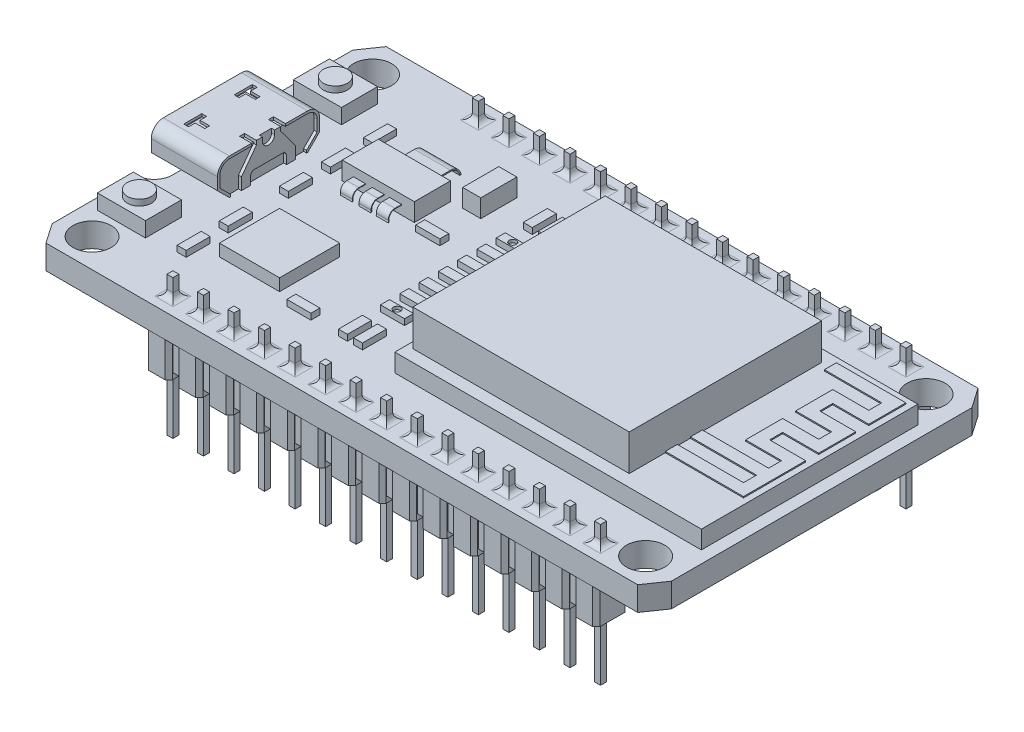
SolidWorks part; units mm, degrees
ref_plane "Alzado" through (0, 0, 0) normal (0, 0, 1) x (1, 0, 0)
ref_plane "Planta" through (0, 0, 0) normal (0, 1, 0) x (1, 0, 0)
ref_plane "Vista lateral" through (0, 0, 0) normal (1, 0, 0) x (0, 0, -1)
sketch "Croquis1" plane through (0, 0, 0) normal (0, 1, 0) x (1, 0, 0)
  line L1 (25.75, 14.15) -> (-25.75, 14.15)
  line L2 (25.75, 14.15) -> (25.75, -14.15)
  line L3 (25.75, -14.15) -> (-25.75, -14.15)
  line L4 (-25.75, 14.15) -> (-25.75, -14.15)
  line L5 (25.75, 14.15) -> (-25.75, -14.15) construction
  line L6 (25.75, -14.15) -> (-25.75, 14.15) construction
  point P0 (0, 0)
  dimension "D1" = 28.3
  dimension "D2" = 51.5
extrude "Saliente-Extruir1" add sketch "Croquis1" along normal blind 2
sketch "Croquis2" plane through (0, 2, 0) normal (0, 1, 0) x (1, 0, 0)
  line L0 (-23.1625, 11.5625) -> (22.875, 11.5625) construction
  line L1 (-23.1625, 11.5625) -> (-25.75, 11.5625) construction
  line L2 (-25.75, 14.15) -> (-25.75, -14.15) construction
  line L3 (-25.75, 11.5625) -> (-24.75, 11.5625) construction
  line L4 (24.4625, 11.5625) -> (25.75, 11.5625) construction
  line L5 (25.75, -14.15) -> (25.75, 14.15) construction
  line L6 (-23.1625, 13.15) -> (-23.1625, 14.15) construction
  line L8 (-23.1625, 11.5625) -> (-23.1625, -11.7625) construction
  line L9 (-23.1625, -11.7625) -> (22.875, -11.7625) construction
  line L10 (25.75, 14.15) -> (-25.75, 14.15) construction
  circle A0 centre (-23.1625, 11.5625) radius 1.5875
  circle A1 centre (22.875, 11.5625) radius 1.5875
  circle A2 centre (-23.1625, -11.7625) radius 1.5875
  circle A3 centre (22.875, -11.7625) radius 1.5875
  point P6 (-0.1437, 11.5625)
  dimension "D1" = 3.175
  dimension "D3" = 1
  dimension "D2" = 46.0375
  dimension "D4" = 1.2875
  dimension "D5" = 23.325
  dimension "D6" = 1
extrude "Cortar-Extruir1" cut sketch "Croquis2" against normal blind 2
sketch "Croquis13" plane through (0, 2, 0) normal (0, 1, 0) x (1, 0, 0)
  line L0 (25.75, 12.5) -> (25.75, -12.5)
  line L1 (25.75, -14.15) -> (25.75, 14.15) construction
  line L2 (-24.6062, -14.15) -> (24.6062, -14.15)
  line L3 (-25.75, -14.15) -> (25.75, -14.15) construction
  line L4 (-24.6062, 14.15) -> (24.6062, 14.15)
  line L5 (25.75, 14.15) -> (-25.75, 14.15) construction
  line L6 (24.6062, 14.15) -> (25.75, 12.5)
  line L7 (25.75, -12.5) -> (24.6062, -14.15)
  line L8 (-25.75, 12.5) -> (-25.75, 5.5)
  line L10 (-25.75, 14.15) -> (-25.75, -14.15) construction
  line L11 (-24.6062, 14.15) -> (-25.75, 12.5)
  line L12 (-25.75, -12.5) -> (-24.6062, -14.15)
  line L13 (-24.25, 4) -> (-24.25, -4)
  line L14 (-25.75, -5.5) -> (-25.75, -12.5)
  arc A0 (-24.25, 4) -> (-25.75, 5.5) centre (-25.75, 4) ccw
  arc A1 (-25.75, -5.5) -> (-24.25, -4) centre (-25.75, -4) ccw
  point P5 (25.75, 0)
  point P11 (0, -14.15)
  point P16 (0, 14.15)
  point P19 (-25.75, 0)
  point P24 (-24.25, 0)
  dimension "D1" = 25
  dimension "D2" = 49.2125
  dimension "D3" = 25
  dimension "D4" = 8
  dimension "D5" = 1.5
extrude "Cortar-Extruir2" cut sketch "Croquis13" against normal blind 3 flip side to cut
sketch "Croquis3" plane through (0, 2, 0) normal (0, 1, 0) x (1, 0, 0)
  line L0 (25.75, -12.5) -> (25.75, 12.5) construction
  line L1 (-0.75, -9) -> (24.75, -9)
  line L2 (-0.75, -9) -> (-0.75, 9)
  line L3 (-0.75, 9) -> (24.75, 9)
  line L4 (24.75, -9) -> (24.75, 9)
  line L5 (-0.75, -9) -> (24.75, 9) construction
  line L6 (-0.75, 9) -> (24.75, -9) construction
  point P0 (12, 0)
  dimension "D1" = 18
  dimension "D2" = 25.5
  dimension "D3" = 1
extrude "Saliente-Extruir2" add sketch "Croquis3" along normal blind 1.5
sketch "Croquis4" plane through (0, 3.5, 0) normal (0, 1, 0) x (1, 0, 0)
  line L0 (17.75, 0) -> (24.75, 0) construction
  line L1 (17.75, 8) -> (-0.25, 8)
  line L2 (17.75, 8) -> (17.75, -8)
  line L3 (17.75, -8) -> (-0.25, -8)
  line L4 (-0.25, 8) -> (-0.25, -8)
  line L5 (17.75, 8) -> (-0.25, -8) construction
  line L6 (17.75, -8) -> (-0.25, 8) construction
  line L7 (24.75, -9) -> (24.75, 9) construction
  point P0 (8.75, 0)
  dimension "D1" = 16
  dimension "D2" = 18
  dimension "D3" = 7
extrude "Saliente-Extruir3" add sketch "Croquis4" along normal blind 3
sketch "Croquis5" plane through (0, 2, 0) normal (0, 1, 0) x (1, 0, 0)
  line L0 (-15.75, 12.7) -> (-15.25, 12.7) construction
  line L2 (-15.25, 12.95) -> (-15.75, 12.95)
  line L3 (-15.25, 12.95) -> (-15.25, 12.45)
  line L4 (-15.25, 12.45) -> (-15.75, 12.45)
  line L5 (-15.75, 12.95) -> (-15.75, 12.45)
  line L6 (-15.25, 12.95) -> (-15.75, 12.45) construction
  line L7 (-15.25, 12.45) -> (-15.75, 12.95) construction
  line L63 (-15.75, 12.7) -> (-25.75, 12.7) construction
  line L64 (-15.5, -12.7) -> (-15.5, 12.7) construction
  line L65 (-25.75, 12.5) -> (-25.75, 5.5) construction
  line L70 (-15.25, -12.45) -> (-15.75, -12.45)
  line L71 (-15.25, -12.45) -> (-15.25, -12.95)
  line L132 (-15.25, -12.95) -> (-15.75, -12.95)
  line L133 (-15.75, -12.45) -> (-15.75, -12.95)
  line L134 (-15.25, -12.45) -> (-15.75, -12.95) construction
  line L135 (-15.25, -12.95) -> (-15.75, -12.45) construction
  point P2 (-15.5, 12.7)
  point P13 (-15.5, 0)
  dimension "D1" = 25.4
  dimension "D2" = 0.5
  dimension "D3" = 0.5
  dimension "D5" = 10
extrude "Saliente-Extruir4" add sketch "Croquis5" against normal blind 10 and the other way blind 1.5875
sketch "Croquis6" plane through (0, 0, 0) normal (0, -1, 0) x (1, 0, 0)
  line L0 (-15.25, -12.95) -> (-15.75, -12.45) construction
  line L1 (-15.25, 12.45) -> (-15.75, 12.95) construction
  line L2 (-15.75, -12.45) -> (-15.25, -12.45) construction
  line L3 (-15.75, 12.95) -> (-15.25, 12.95) construction
  line L4 (-15.75, 12.95) -> (-15.25, 12.95) construction
  line L5 (-16.5, -11.35) -> (-14.5, -11.35)
  line L6 (-16.5, -11.35) -> (-16.5, -14.05)
  line L7 (-16.5, -14.05) -> (-14.5, -14.05)
  line L8 (-14.5, -11.35) -> (-14.5, -14.05)
  line L9 (-16.5, -11.35) -> (-14.5, -14.05) construction
  line L10 (-16.5, -14.05) -> (-14.5, -11.35) construction
  line L12 (-14.5, 14.05) -> (-16.5, 14.05)
  line L13 (-14.5, 14.05) -> (-14.5, 11.35)
  line L14 (-14.5, 11.35) -> (-16.5, 11.35)
  line L15 (-16.5, 14.05) -> (-16.5, 11.35)
  line L16 (-14.5, 14.05) -> (-16.5, 11.35) construction
  line L17 (-14.5, 11.35) -> (-16.5, 14.05) construction
  point P4 (-15.5, -12.7)
  point P5 (-15.5, -12.7)
  point P8 (-15.5, -12.7)
  point P19 (-15.5, 12.7)
  point P20 (-15.5, 12.7)
  dimension "D1" = 2.7
  dimension "D2" = 2
extrude "Saliente-Extruir5" add sketch "Croquis6" along normal blind 3
chamfer "Chaflán1" distance 0.3 angle 45 8 edges at (-16.5, -1.5, -14.05) (-16.5, -1.5, -11.35) (-14.5, -1.5, -11.35) (-14.5, -1.5, -14.05) (-16.5, -1.5, 11.35) (-14.5, -1.5, 11.35) (-14.5, -1.5, 14.05) (-16.5, -1.5, 14.05)
sketch "Croquis7" plane through (0, 0, 0) normal (0, -1, 0) x (1, 0, 0)
  line L0 (-14.5, -12.7) -> (-39.3073, -12.7) construction
  line L1 (-14.5, -13.75) -> (-14.5, -11.65) construction
fillet "Redondeo2" radius 0.5 8 edges at (-15.75, 2, -12.7) (-15.5, 2, -12.45) (-15.25, 2, -12.7) (-15.5, 2, -12.95) (-15.25, 2, 12.7) (-15.5, 2, 12.95) (-15.5, 2, 12.45) (-15.75, 2, 12.7)
pattern_linear "MatrizL1" count 15 spacing 2.54 along (1, 0, 0) of "Saliente-Extruir5", "Chaflán1", "Saliente-Extruir4", "Redondeo2"
sketch "Croquis8" plane through (0, 0, 0) normal (0, -1, 0) x (1, 0, 0)
  line L0 (21.06, -13.75) -> (21.06, -11.65) construction
  line L8 (-16.5, -13.7) -> (21.06, -13.7)
  line L9 (-16.5, -13.7) -> (-16.5, -11.7)
  line L10 (-16.5, -11.7) -> (21.06, -11.7)
  line L11 (21.06, -13.7) -> (21.06, -11.7)
  line L12 (-16.5, -13.7) -> (21.06, -11.7) construction
  line L13 (-16.5, -11.7) -> (21.06, -13.7) construction
  line L14 (2.28, -12.95) -> (2.28, -12.45) construction
  line L15 (2.53, -12.95) -> (2.03, -12.95) construction
  line L16 (2.03, -12.45) -> (2.53, -12.45) construction
  line L17 (2.53, 12.7) -> (2.03, 12.7) construction
  line L18 (2.53, 12.95) -> (2.53, 12.45) construction
  line L19 (2.03, 12.45) -> (2.03, 12.95) construction
  line L20 (21.06, 11.65) -> (21.06, 13.75) construction
  line L21 (-16.5, 11.7) -> (21.06, 11.7)
  line L22 (-16.5, 11.7) -> (-16.5, 13.7)
  line L23 (-16.5, 13.7) -> (21.06, 13.7)
  line L24 (21.06, 11.7) -> (21.06, 13.7)
  line L25 (-16.5, 11.7) -> (21.06, 13.7) construction
  line L26 (-16.5, 13.7) -> (21.06, 11.7) construction
  point P0 (2.28, -12.7)
  point P6 (2.28, -12.7)
  point P14 (2.28, 12.7)
  point P15 (2.28, -12.7)
  point P22 (2.28, 12.7)
  dimension "D1" = 2
extrude "Saliente-Extruir6" add sketch "Croquis8" along normal blind 2.5
sketch "Croquis12" plane through (0, 2, 0) normal (0, 1, 0) x (1, 0, 0)
  line L0 (-25.75, 14.15) -> (-25.75, -14.15) construction
  line L1 (-20.25, 4.25) -> (-25.75, 4.25)
  line L2 (-20.25, 4.25) -> (-20.25, -4.25)
  line L3 (-20.25, -4.25) -> (-25.75, -4.25)
  line L4 (-25.75, 4.25) -> (-25.75, -4.25)
  line L5 (-20.25, 4.25) -> (-25.75, -4.25) construction
  line L6 (-20.25, -4.25) -> (-25.75, 4.25) construction
  point P0 (-23, 0)
  dimension "D1" = 8.5
  dimension "D2" = 5.5
extrude "Saliente-Extruir9" add sketch "Croquis12" along normal blind 3
fillet "Redondeo1" radius 1 2 edges at (-23, 5, 4.25) (-23, 5, -4.25)
sketch "Croquis14" plane through (-25.75, 0, 0) normal (-1, 0, 0) x (0, 0, 1)
  line L0 (4.25, 2) -> (3.25, 2) construction
  line L1 (-4, 2) -> (4, 2) construction
  line L2 (3.25, 2) -> (4.25, 3)
  line L3 (4.25, 4) -> (4.25, 2) construction
  line L4 (-4.25, 2) -> (-3.25, 2) construction
  line L5 (-3.25, 2) -> (-4.25, 3)
  line L6 (-4.25, 4) -> (-4.25, 2) construction
  line L7 (-4.25, 3) -> (-4.25, 2)
  line L8 (-4.25, 2) -> (-3.25, 2)
  line L10 (4.25, 3) -> (4.25, 2)
  line M3 (4.25, 2) -> (4.25, 4)
  line M7 (-4.25, 4) -> (-4.25, 2)
  line M8 (-4.25, 2) -> (4.25, 2)
  dimension "D1" = 1
  dimension "D2" = 1
extrude "Cortar-Extruir3" cut sketch "Croquis14" against normal blind 6 contours L5 M8 M7 | L2 M8 M3
sketch "Croquis15" plane through (-25.75, 0, 0) normal (-1, 0, 0) x (0, 0, 1)
  line L0 (-3.25, 2) -> (3.25, 2) construction
  line L1 (3.25, 2) -> (4.25, 3) construction
  line L2 (4.25, 3) -> (4.25, 4) construction
  line L3 (-3.25, 5) -> (3.25, 5) construction
  line L4 (3.25, 5) -> (-3.25, 5) construction
  line L5 (-4.25, 4) -> (-4.25, 3) construction
  line L6 (-4.25, 3) -> (-3.25, 2) construction
  line L7 (-3.25, 2) -> (3.25, 2) construction
  line L8 (-3.1672, 2.2) -> (3.1672, 2.2)
  line L9 (3.1672, 2.2) -> (4.05, 3.0828)
  line L10 (4.05, 3.0828) -> (4.05, 4)
  line L11 (3.25, 4.8) -> (-3.25, 4.8)
  line L12 (-4.05, 4) -> (-4.05, 3.0828)
  line L13 (-4.05, 3.0828) -> (-3.1672, 2.2)
  line L14 (-3.1672, 2.2) -> (3.1672, 2.2)
  line L15 (-3.25, 2.2) -> (3.25, 2.2) construction
  line L16 (-3.25, 2.2) -> (3.25, 2.2) construction
  line L17 (-4.05, 3.0828) -> (-3.1086, 2.1414) construction
  line L18 (3.1086, 2.1414) -> (4.05, 3.0828) construction
  arc A0 (-3.25, 5) -> (-4.25, 4) centre (-3.25, 4) ccw construction
  arc A1 (4.25, 4) -> (3.25, 5) centre (3.25, 4) ccw construction
  arc A2 (-3.25, 5) -> (-4.25, 4) centre (-3.25, 4) ccw construction
  arc A3 (4.05, 4) -> (3.25, 4.8) centre (3.25, 4) ccw
  arc A4 (-3.25, 4.8) -> (-4.05, 4) centre (-3.25, 4) ccw
  point P4 (3.25, 5)
  point P9 (-3.25, 5)
  point P10 (-4.25, 4)
  dimension "D1" = 0.2
extrude "Cortar-Extruir4" cut sketch "Croquis15" against normal blind 4 contours L11 A4 L12 L13 L8 L9 L10 A3
sketch "Croquis16" plane through (-20.25, 0, 0) normal (1, 0, 0) x (0, 0, -1)
  line L0 (-3.25, 2) -> (-3.1672, 2) construction
  line L1 (-1.5, 2.7501) -> (-1.5, 2)
  line L3 (-4.25, 3) -> (-2.25, 3) construction
  line L4 (-2.25, 3) -> (-1, 4.6673)
  line L5 (-0.5, 5) -> (0.5, 5)
  line L6 (-3.25, 5) -> (3.25, 5) construction
  line L7 (3.1672, 2.2) -> (3.1672, 2)
  line L8 (-0.5, 5) -> (-0.5, 4.6673)
  line L9 (0, 5) -> (0, 2.5205) construction
  line L10 (-1, 4.6673) -> (-1, 5)
  line L11 (-3.25, 2) -> (-4.25, 3) construction
  line L12 (-4.25, 3) -> (-4.25, 4) construction
  line L13 (-3.25, 5) -> (-1.4111, 5) construction
  line L19 (-3.1672, 2.2) -> (-4.05, 3.0828)
  line L20 (-4.05, 3.0828) -> (-4.05, 4)
  line L21 (-2.45, 3.0666) -> (-1.2, 4.7339) construction
  line L22 (-1.2, 4.7339) -> (-1.2, 4.8) construction
  line L23 (-2.45, 2.2) -> (-2.45, 3.0666) construction
  line L25 (-3.1672, 2.2) -> (-2.45, 2.2) construction
  line L26 (-2.25, 2) -> (-2.25, 3) construction
  line L27 (-3.25, 4.8) -> (-1.2, 4.8) construction
  line L28 (-3.25, 4.8) -> (-1.4111, 4.8)
  line L31 (-3.25, 5) -> (-1, 5) construction
  line L33 (-1.4111, 4.8) -> (-1.4111, 5)
  line L34 (-1.4111, 5) -> (-1, 5)
  line L35 (-1.5, 2.7501) -> (-1.3169, 2.9943)
  line L36 (-1.3169, 2.9943) -> (1.3169, 2.9943)
  line L37 (-1.5, 2.7501) -> (-0.3999, 4.2174) construction
  line L39 (3.25, 5) -> (1.4111, 5) construction
  line L40 (4.25, 3) -> (4.25, 4) construction
  line L41 (3.25, 2) -> (4.25, 3) construction
  line L43 (4.25, 3) -> (2.25, 3) construction
  line L44 (3.25, 2) -> (3.1672, 2) construction
  line L45 (1.5, 2.7501) -> (1.3169, 2.9943)
  line L46 (1.4111, 5) -> (1, 5)
  line L47 (1.4111, 4.8) -> (1.4111, 5)
  line L49 (3.25, 4.8) -> (1.4111, 4.8)
  line L51 (4.05, 3.0828) -> (4.05, 4)
  line L52 (3.1672, 2.2) -> (4.05, 3.0828)
  line L53 (1, 4.6673) -> (1, 5)
  line L54 (0.5, 5) -> (0.5, 4.6673)
  line L55 (2.25, 3) -> (1, 4.6673)
  line L57 (3.1672, 2) -> (2.25, 2)
  line L58 (2.25, 3) -> (2.25, 2)
  line L59 (-3.1672, 2.2) -> (-3.1672, 2)
  line L60 (-2.25, 3) -> (-2.25, 2)
  line L61 (-3.25, 2) -> (3.25, 2) construction
  line L62 (-3.25, 2) -> (-2.25, 2) construction
  line L63 (-2.25, 2.2) -> (-2.25, 3) construction
  line L64 (-2.25, 2) -> (-3.1672, 2)
  line L66 (1.5, 2) -> (-1.5, 2)
  line L68 (-1.5, 2.2) -> (-1.5, 2.7501) construction
  line L69 (1.5, 2.7501) -> (1.5, 2)
  arc A0 (-0.5, 4.6673) -> (0.5, 4.6673) centre (0, 4.6673) ccw
  arc A1 (-4.25, 4) -> (-3.25, 5) centre (-3.25, 4) cw construction
  arc A2 (-4.05, 4) -> (-3.25, 4.8) centre (-3.25, 4) cw
  arc A3 (4.25, 4) -> (3.25, 5) centre (3.25, 4) ccw construction
  arc A4 (4.05, 4) -> (3.25, 4.8) centre (3.25, 4) ccw
  point P50 (0, 5)
  point P57 (0, 2.2)
  point P58 (0, 2.9943)
  dimension "D2" = 0.5
  dimension "D3" = 0.5
  dimension "D4" = 0.2
  dimension "D5" = 0.75
extrude "Cortar-Extruir5" cut sketch "Croquis16" against normal blind 0.25
sketch "Croquis17" plane through (0, 5, 0) normal (0, 1, 0) x (1, 0, 0)
  line L1 (-20.25, -1.4111) -> (-21.25, -1.4111)
  line L2 (-20.25, -1.4111) -> (-20.25, -1)
  line L3 (-20.25, -1) -> (-21.25, -1)
  line L4 (-21.25, -1.4111) -> (-21.25, -1)
  line L5 (-20.25, 1) -> (-21.25, 1)
  line L6 (-20.25, 1) -> (-20.25, 1.4111)
  line L7 (-20.25, 1.4111) -> (-21.25, 1.4111)
  line L8 (-21.25, 1) -> (-21.25, 1.4111)
  dimension "D1" = 1
extrude "Cortar-Extruir6" cut sketch "Croquis17" against normal blind 0.25
sketch "Croquis18" plane through (-21.75, 0, 0) normal (-1, 0, 0) x (0, 0, 1)
  line L1 (-2.8448, 3.4346) -> (2.8448, 3.4346)
  line L2 (-2.8448, 3.4346) -> (-2.8448, 4.1935)
  line L3 (-2.8448, 4.1935) -> (2.8448, 4.1935)
  line L4 (2.8448, 3.4346) -> (2.8448, 4.1935)
  line L5 (-2.8448, 3.4346) -> (2.8448, 4.1935) construction
  line L6 (-2.8448, 4.1935) -> (2.8448, 3.4346) construction
  point P0 (0, 3.8141)
extrude "Saliente-Extruir10" add sketch "Croquis18" along normal blind 3.25
sketch "Croquis19" plane through (0, 2, 0) normal (0, 1, 0) x (1, 0, 0)
  line L0 (-24.6062, -14.15) -> (24.6062, -14.15) construction
  line L1 (-24.8373, -6.65) -> (-20.8373, -6.65)
  line L2 (-24.8373, -6.65) -> (-24.8373, -9.65)
  line L3 (-24.8373, -9.65) -> (-20.8373, -9.65)
  line L4 (-20.8373, -6.65) -> (-20.8373, -9.65)
  line L5 (-24.8373, -6.65) -> (-20.8373, -9.65) construction
  line L6 (-24.8373, -9.65) -> (-20.8373, -6.65) construction
  line L7 (24.6062, 14.15) -> (-24.6062, 14.15) construction
  line L8 (-24.8373, 9.65) -> (-20.8373, 9.65)
  line L9 (-24.8373, 9.65) -> (-24.8373, 6.65)
  line L10 (-24.8373, 6.65) -> (-20.8373, 6.65)
  line L11 (-20.8373, 9.65) -> (-20.8373, 6.65)
  line L12 (-24.8373, 9.65) -> (-20.8373, 6.65) construction
  line L13 (-24.8373, 6.65) -> (-20.8373, 9.65) construction
  point P0 (-22.8373, -8.15)
  point P7 (-22.8373, 8.15)
  dimension "D1" = 4.5
  dimension "D2" = 3
  dimension "D3" = 4
  dimension "D4" = 3
  dimension "D5" = 4.5
extrude "Saliente-Extruir11" add sketch "Croquis19" along normal blind 1.25
sketch "Croquis22" plane through (0, 3.25, 0) normal (0, 1, 0) x (1, 0, 0)
  line L0 (-22.8373, 9.65) -> (-22.8373, 6.65) construction
  line L1 (-20.8373, 9.65) -> (-24.8373, 9.65) construction
  line L2 (-24.8373, 6.65) -> (-20.8373, 6.65) construction
  line L3 (-22.8373, -6.65) -> (-22.8373, -9.65) construction
  line L4 (-20.8373, -6.65) -> (-24.8373, -6.65) construction
  line L5 (-24.8373, -9.65) -> (-20.8373, -9.65) construction
  circle A0 centre (-22.8373, 8.15) radius 1
  circle A1 centre (-22.8373, -8.15) radius 1
  dimension "D1" = 2
  dimension "D2" = 2
extrude "Saliente-Extruir13" add sketch "Croquis22" along normal blind 0.5
sketch "Croquis23" plane through (0, 2, 0) normal (0, 1, 0) x (1, 0, 0)
  line L0 (-18.125, 8.15) -> (-18.125, -0.85) construction
  line L1 (-18.125, 8.15) -> (-18.125, 14.15) construction
  line L2 (-18.5, 4.65) -> (-17.75, 4.65)
  line L3 (-18.5, 4.65) -> (-18.5, 2.65)
  line L4 (-18.5, 2.65) -> (-17.75, 2.65)
  line L5 (-17.75, 4.65) -> (-17.75, 2.65)
  line L6 (-18.5, 4.65) -> (-17.75, 2.65) construction
  line L7 (-18.5, 2.65) -> (-17.75, 4.65) construction
  line L8 (-17.75, 6.15) -> (-18.5, 6.15)
  line L9 (-17.75, 6.15) -> (-17.75, 8.15)
  line L10 (-17.75, 8.15) -> (-18.5, 8.15)
  line L11 (-18.5, 6.15) -> (-18.5, 8.15)
  line L12 (-17.75, 6.15) -> (-18.5, 8.15) construction
  line L13 (-17.75, 8.15) -> (-18.5, 6.15) construction
  line L14 (-17.75, 1.15) -> (-18.5, 1.15)
  line L15 (-17.75, 1.15) -> (-17.75, -0.85)
  line L16 (-17.75, -0.85) -> (-18.5, -0.85)
  line L17 (-18.5, 1.15) -> (-18.5, -0.85)
  line L18 (-17.75, 1.15) -> (-18.5, -0.85) construction
  line L19 (-17.75, -0.85) -> (-18.5, 1.15) construction
  line L20 (24.6062, 14.15) -> (-24.6062, 14.15) construction
  line L21 (-25.75, 12.5) -> (-25.75, 5.5) construction
  line L22 (-18.125, -3.85) -> (-18.125, -9.35) construction
  line L23 (-18.5, -7.35) -> (-17.75, -7.35)
  line L24 (-18.5, -7.35) -> (-18.5, -9.35)
  line L25 (-18.5, -9.35) -> (-17.75, -9.35)
  line L26 (-17.75, -7.35) -> (-17.75, -9.35)
  line L27 (-18.5, -7.35) -> (-17.75, -9.35) construction
  line L28 (-18.5, -9.35) -> (-17.75, -7.35) construction
  line L29 (-17.75, -5.85) -> (-18.5, -5.85)
  line L30 (-17.75, -5.85) -> (-17.75, -3.85)
  line L31 (-17.75, -3.85) -> (-18.5, -3.85)
  line L32 (-18.5, -5.85) -> (-18.5, -3.85)
  line L33 (-17.75, -5.85) -> (-18.5, -3.85) construction
  line L34 (-17.75, -3.85) -> (-18.5, -5.85) construction
  line L39 (-4.75, 5.1875) -> (-4.75, -4.8125) construction
  line L40 (-5.75, 3.5833) -> (-3.75, 3.5833)
  line L41 (-5.75, 4.4375) -> (-3.75, 4.4375)
  line L42 (-5.75, 4.4375) -> (-5.75, 5.1875)
  line L43 (-5.75, 5.1875) -> (-3.75, 5.1875)
  line L44 (-3.75, 4.4375) -> (-3.75, 5.1875)
  line L45 (-5.75, 4.4375) -> (-3.75, 5.1875) construction
  line L46 (-5.75, 5.1875) -> (-3.75, 4.4375) construction
  line L47 (-5.75, 2.8333) -> (-3.75, 2.8333)
  line L48 (-5.75, 2.8333) -> (-5.75, 3.5833)
  line L49 (-3.75, 2.8333) -> (-3.75, 3.5833)
  line L50 (-5.75, 1.9792) -> (-3.75, 1.9792)
  line L51 (-5.75, 1.2292) -> (-3.75, 1.2292)
  line L52 (-5.75, 1.2292) -> (-5.75, 1.9792)
  line L53 (-3.75, 1.2292) -> (-3.75, 1.9792)
  line L54 (-5.75, 0.375) -> (-3.75, 0.375)
  line L55 (-5.75, -0.375) -> (-3.75, -0.375)
  line L56 (-5.75, -0.375) -> (-5.75, 0.375)
  line L57 (-3.75, -0.375) -> (-3.75, 0.375)
  line L58 (-5.75, -1.2292) -> (-3.75, -1.2292)
  line L59 (-5.75, -1.9792) -> (-3.75, -1.9792)
  line L60 (-5.75, -1.9792) -> (-5.75, -1.2292)
  line L61 (-3.75, -1.9792) -> (-3.75, -1.2292)
  line L62 (-5.75, -2.8333) -> (-3.75, -2.8333)
  line L63 (-5.75, -3.5833) -> (-3.75, -3.5833)
  line L64 (-5.75, -3.5833) -> (-5.75, -2.8333)
  line L65 (-3.75, -3.5833) -> (-3.75, -2.8333)
  line L66 (-5.75, -4.4375) -> (-3.75, -4.4375)
  line L67 (-5.75, -5.1875) -> (-3.75, -5.1875)
  line L68 (-5.75, -5.1875) -> (-5.75, -4.4375)
  line L69 (-3.75, -5.1875) -> (-3.75, -4.4375)
  line L70 (-0.75, 9) -> (-0.75, -9) construction
  line L72 (-4.5, -6.6875) -> (-3.75, -6.6875)
  line L73 (-4.5, -6.6875) -> (-4.5, -8.6875)
  line L74 (-4.5, -8.6875) -> (-3.75, -8.6875)
  line L75 (-3.75, -6.6875) -> (-3.75, -8.6875)
  line L76 (-4.5, -6.6875) -> (-3.75, -8.6875) construction
  line L77 (-4.5, -8.6875) -> (-3.75, -6.6875) construction
  line L79 (-5.75, -6.6875) -> (-5, -6.6875)
  line L80 (-5.75, -6.6875) -> (-5.75, -8.6875)
  line L81 (-5.75, -8.6875) -> (-5, -8.6875)
  line L82 (-5, -6.6875) -> (-5, -8.6875)
  line L83 (-5.75, -6.6875) -> (-5, -8.6875) construction
  line L84 (-5.75, -8.6875) -> (-5, -6.6875) construction
  line L85 (-4.75, 5.1875) -> (-4.75, -5.1875) construction
  line L86 (-4.75, 2.8333) -> (-4.75, 1.9792) construction
  line L87 (-4.5, 8.6875) -> (-3.75, 8.6875)
  line L88 (-4.5, 8.6875) -> (-4.5, 6.6875)
  line L89 (-4.5, 6.6875) -> (-3.75, 6.6875)
  line L90 (-3.75, 8.6875) -> (-3.75, 6.6875)
  line L91 (-4.5, 8.6875) -> (-3.75, 6.6875) construction
  line L92 (-4.5, 6.6875) -> (-3.75, 8.6875) construction
  line L93 (-5.75, 8.6875) -> (-5, 8.6875)
  line L94 (-5.75, 8.6875) -> (-5.75, 6.6875)
  line L95 (-5.75, 6.6875) -> (-5, 6.6875)
  line L96 (-5, 8.6875) -> (-5, 6.6875)
  line L97 (-5.75, 8.6875) -> (-5, 6.6875) construction
  line L98 (-5.75, 6.6875) -> (-5, 8.6875) construction
  line L99 (-10.0373, -7.9375) -> (-8.0373, -7.9375)
  line L100 (-10.0373, -7.9375) -> (-10.0373, -8.6875)
  line L101 (-10.0373, -8.6875) -> (-8.0373, -8.6875)
  line L102 (-8.0373, -7.9375) -> (-8.0373, -8.6875)
  line L103 (-10.0373, -7.9375) -> (-8.0373, -8.6875) construction
  line L104 (-10.0373, -8.6875) -> (-8.0373, -7.9375) construction
  line L106 (-10.0373, 2.7812) -> (-8.0373, 2.7812)
  line L107 (-10.0373, 2.7812) -> (-10.0373, 2.0312)
  line L108 (-10.0373, 2.0312) -> (-8.0373, 2.0312)
  line L109 (-8.0373, 2.7812) -> (-8.0373, 2.0312)
  line L110 (-10.0373, 2.7812) -> (-8.0373, 2.0312) construction
  line L111 (-10.0373, 2.0312) -> (-8.0373, 2.7812) construction
  point P2 (-18.125, 3.65)
  point P7 (-18.125, 7.15)
  point P12 (-18.125, 0.15)
  point P24 (-18.125, -8.35)
  point P29 (-18.125, -4.85)
  point P35 (-4.75, 4.8125)
  point P42 (-4.75, 3.2083)
  point P47 (-4.75, 1.6042)
  point P52 (-4.75, 0)
  point P57 (-4.75, -1.6042)
  point P62 (-4.75, -3.2083)
  point P67 (-4.75, -4.8125)
  point P73 (-5.375, -7.6875)
  point P74 (-4.125, -7.6875)
  point P83 (-5.375, 7.6875)
  point P84 (-4.125, 7.6875)
  point P97 (-4.75, 2.4062)
  point P98 (-9.0373, -8.3125)
  point P103 (-9.0373, 2.4062)
  dimension "D1" = 9
  dimension "D2" = 0.75
  dimension "D3" = 2
  dimension "D4" = 6
  dimension "D5" = 8
  dimension "D6" = 2
  dimension "D7" = 2
  dimension "D8" = 1.5
  dimension "D9" = 3
  dimension "D10" = 0.75
  dimension "D11" = 7
  dimension "D12" = 10
  dimension "D13" = 0.75
  dimension "D14" = 4
  dimension "D15" = 0.75
  dimension "D16" = 2
  dimension "D17" = 2
  dimension "D18" = 1.5
  dimension "D19" = 1.5
  dimension "D20" = 0.75
  dimension "D21" = 2
extrude "Saliente-Extruir14" add sketch "Croquis23" along normal blind 0.5
sketch "Croquis26" plane through (0, 2, 0) normal (0, 1, 0) x (1, 0, 0)
  line L0 (-8.0373, -7.9375) -> (-10.0373, -7.9375) construction
  line L1 (-16.3937, -2.9375) -> (-11.3937, -2.9375)
  line L2 (-16.3937, -2.9375) -> (-16.3937, -7.9375)
  line L3 (-16.3937, -7.9375) -> (-11.3937, -7.9375)
  line L4 (-11.3937, -2.9375) -> (-11.3937, -7.9375)
  line L5 (-16.3937, -2.9375) -> (-11.3937, -7.9375) construction
  line L6 (-16.3937, -7.9375) -> (-11.3937, -2.9375) construction
  line L7 (-17.75, -8.35) -> (-10.0373, -8.3125) construction
  line L8 (-17.75, -9.35) -> (-17.75, -7.35) construction
  line L9 (-10.0373, -7.9375) -> (-10.0373, -8.6875) construction
  point P0 (-13.8937, -5.4375)
  point P7 (-13.8937, -8.3312)
  dimension "D1" = 5
  dimension "D2" = 5
extrude "Saliente-Extruir15" add sketch "Croquis26" along normal blind 1
sketch "Croquis27" plane through (0, 2, 0) normal (0, 1, 0) x (1, 0, 0)
  line L0 (-8.0373, 2.7812) -> (-10.0373, 2.7812) construction
  line L1 (-5, 8.6875) -> (-5.75, 8.6875) construction
  line L2 (-9.7873, 8.6875) -> (-8.2873, 8.6875)
  line L3 (-9.7873, 8.6875) -> (-9.7873, 5.6875)
  line L4 (-9.7873, 5.6875) -> (-8.2873, 5.6875)
  line L5 (-8.2873, 8.6875) -> (-8.2873, 5.6875)
  line L6 (-9.7873, 8.6875) -> (-8.2873, 5.6875) construction
  line L7 (-9.7873, 5.6875) -> (-8.2873, 8.6875) construction
  point P0 (-9.0373, 2.7812)
  point P1 (-9.0373, 7.1875)
  dimension "D1" = 1.5
  dimension "D2" = 3
extrude "Saliente-Extruir16" add sketch "Croquis27" along normal blind 1.5
sketch "Croquis28" plane through (0, 2, 0) normal (0, 1, 0) x (1, 0, 0)
  line L0 (-17.75, 8.15) -> (-9.7873, 8.15) construction
  line L1 (-16.7687, 5.65) -> (-10.7687, 5.65)
  line L2 (-16.7687, 5.65) -> (-16.7687, 2.65)
  line L3 (-16.7687, 2.65) -> (-10.7687, 2.65)
  line L4 (-10.7687, 5.65) -> (-10.7687, 2.65)
  line L5 (-16.7687, 5.65) -> (-10.7687, 2.65) construction
  line L6 (-16.7687, 2.65) -> (-10.7687, 5.65) construction
  line L7 (-9.7873, 8.6875) -> (-9.7873, 5.6875) construction
  line L9 (-18.5, 2.65) -> (-17.75, 2.65) construction
  point P0 (-13.7687, 4.15)
  point P10 (-13.7687, 8.15)
  dimension "D1" = 6
  dimension "D2" = 3
extrude "Saliente-Extruir17" add sketch "Croquis28" along normal blind 1.5
sketch "Croquis30" plane through (0, 3.5, 0) normal (0, 1, 0) x (1, 0, 0)
  line L0 (18.4797, 8) -> (23.7544, 8) construction
  line L1 (23.7544, 8) -> (23.7544, 5.9167) construction
  line L2 (23.7544, 5.9167) -> (20.7587, 5.9167) construction
  line L3 (20.7587, 5.9167) -> (20.7587, 3.8333) construction
  line L4 (20.7587, 3.8333) -> (23.7544, 3.8333) construction
  line L5 (23.7544, 3.8333) -> (23.7544, 1.75) construction
  line L6 (23.7544, 1.75) -> (20.7587, 1.75) construction
  line L7 (20.7587, 1.75) -> (20.7587, -0.3333) construction
  line L8 (20.7587, -0.3333) -> (23.7544, -0.3333) construction
  line L9 (23.7544, -0.3333) -> (23.7544, -2.4167) construction
  line L10 (23.7544, -2.4167) -> (23.7544, -4.5) construction
  line L11 (23.7544, -4.5) -> (17.75, -4.5) construction
  line L12 (17.75, -8) -> (17.75, 8) construction
  line L13 (23.7544, -2.4167) -> (17.75, -2.4167) construction
  line L14 (17.75, 8) -> (-0.25, 8) construction
  line L15 (18.4797, 7.5) -> (23.2544, 7.5)
  line L16 (23.2544, 7.5) -> (23.2544, 6.4167)
  line L17 (23.2544, 6.4167) -> (20.2587, 6.4167)
  line L18 (20.2587, 6.4167) -> (20.2587, 3.3333)
  line L19 (20.2587, 3.3333) -> (23.2544, 3.3333)
  line L20 (23.2544, 3.3333) -> (23.2544, 2.25)
  line L21 (23.2544, 2.25) -> (20.2587, 2.25)
  line L22 (20.2587, 2.25) -> (20.2587, -0.8333)
  line L23 (20.2587, -0.8333) -> (23.2544, -0.8333)
  line L24 (23.2544, -0.8333) -> (23.2544, -1.9167)
  line L25 (23.2544, -2.9167) -> (23.2544, -4)
  line L26 (23.2544, -4) -> (17.75, -4)
  line L27 (23.2544, -1.9167) -> (17.75, -1.9167)
  line L28 (18.4797, 8.5) -> (24.2544, 8.5)
  line L29 (24.2544, 8.5) -> (24.2544, 5.4167)
  line L30 (24.2544, 5.4167) -> (21.2587, 5.4167)
  line L31 (21.2587, 5.4167) -> (21.2587, 4.3333)
  line L32 (21.2587, 4.3333) -> (24.2544, 4.3333)
  line L33 (24.2544, 4.3333) -> (24.2544, 1.25)
  line L34 (24.2544, 1.25) -> (21.2587, 1.25)
  line L35 (21.2587, 1.25) -> (21.2587, 0.1667)
  line L36 (21.2587, 0.1667) -> (24.2544, 0.1667)
  line L37 (24.2544, 0.1667) -> (24.2544, -2.4167)
  line L38 (24.2544, -2.4167) -> (24.2544, -5)
  line L39 (24.2544, -5) -> (17.75, -5)
  line L40 (23.2544, -2.9167) -> (17.75, -2.9167)
  line L41 (23.2544, -2.4167) -> (23.2544, -4) construction
  line L42 (23.2544, -0.8333) -> (23.2544, -2.4167) construction
  line L43 (23.7544, -1.9167) -> (17.75, -1.9167) construction
  line L44 (23.7544, -2.9167) -> (17.75, -2.9167) construction
  line L45 (18.4797, 8.5) -> (18.4797, 7.5)
  line L46 (17.75, -1.9167) -> (17.75, -2.9167)
  line L47 (17.75, -4) -> (17.75, -5)
  point P17 (21.1171, 8)
  dimension "D1" = 12.5
  dimension "D2" = 2.0833
  dimension "D3" = 0.5
  dimension "D4" = 0.5
extrude "Saliente-Extruir18" add sketch "Croquis30" along normal blind 0.1
sketch "Croquis31" plane through (0, 2.5, 0) normal (0, 1, 0) x (1, 0, 0)
  line L0 (-4.75, 5.1875) -> (-4.75, 4.4375) construction
  line L1 (-3.75, 5.1875) -> (-5.75, 5.1875) construction
  line L2 (-5.75, 4.4375) -> (-3.75, 4.4375) construction
  line L3 (-4.75, -4.4375) -> (-4.75, -5.1875) construction
  line L4 (-3.75, -4.4375) -> (-5.75, -4.4375) construction
  line L5 (-5.75, -5.1875) -> (-3.75, -5.1875) construction
  circle A0 centre (-4.75, 4.8125) radius 0.3
  circle A1 centre (-4.75, -4.8125) radius 0.3
  dimension "D1" = 0.6
extrude "Cortar-Extruir7" cut sketch "Croquis31" against normal blind 0.25
ref_plane "Plano2" through (-13.7687, 0, 0) normal (-1, 0, 0) x (0, 0, 1)
sketch "Croquis32" plane through (-13.7687, 0, 0) normal (-1, 0, 0) x (0, 0, 1)
  line L0 (-5.65, 2.75) -> (-7.1537, 2.75)
  line L2 (-5.65, 3.5) -> (-5.65, 2) construction
  arc A0 (-7.1537, 2.75) -> (-8.0258, 1.8778) centre (-7.1537, 1.8778) ccw
sketch "Croquis33" plane through (0, 0, -5.65) normal (0, 0, -1) x (-1, 0, 0)
  line L0 (13.7687, 1.8778) -> (13.7687, 2.75) construction
  line L1 (12.2687, 2.6649) -> (15.2687, 2.6649)
  line L2 (12.2687, 2.6649) -> (12.2687, 2.7649)
  line L3 (12.2687, 2.7649) -> (15.2687, 2.7649)
  line L4 (15.2687, 2.6649) -> (15.2687, 2.7649)
  line L5 (12.2687, 2.6649) -> (15.2687, 2.7649) construction
  line L6 (12.2687, 2.7649) -> (15.2687, 2.6649) construction
  point P0 (13.7687, 2.7149)
  dimension "D1" = 3
  dimension "D2" = 0.1
sweep "Barrer1" add profiles "Croquis33" path "Croquis32"
sketch "Croquis34" plane through (-13.7687, 0, 0) normal (-1, 0, 0) x (0, 0, 1)
  line L0 (-2.65, 2.75) -> (-2.0959, 2.75)
  line L1 (-2.65, 3.5) -> (-2.65, 2) construction
  arc A0 (-2.0959, 2.75) -> (-1.5811, 2.1692) centre (-2.0959, 2.2314) cw
  arc A1 (-1.5811, 2.1692) -> (-1.0864, 1.8337) centre (-1.2473, 2.1289) ccw
sketch "Croquis35" plane through (0, 0, -2.65) normal (0, 0, 1) x (1, 0, 0)
  line L0 (-13.7687, 0.825) -> (-13.7687, -0.825) construction
  line L1 (-14.2687, 2.7235) -> (-13.2687, 2.7235)
  line L2 (-14.2687, 2.7235) -> (-14.2687, 2.7735)
  line L3 (-14.2687, 2.7735) -> (-13.2687, 2.7735)
  line L4 (-13.2687, 2.7235) -> (-13.2687, 2.7735)
  line L5 (-14.2687, 2.7235) -> (-13.2687, 2.7735) construction
  line L6 (-14.2687, 2.7735) -> (-13.2687, 2.7235) construction
  line L7 (-16.3937, 2.7235) -> (-14.2687, 2.7485) construction
  line L8 (-16.3937, 3) -> (-16.3937, 2) construction
  line L9 (-13.2687, 2.7485) -> (-11.3937, 2.7485) construction
  line L10 (-15.8312, 2.711) -> (-14.8312, 2.711)
  line L11 (-15.8312, 2.711) -> (-15.8312, 2.761)
  line L12 (-15.8312, 2.761) -> (-14.8312, 2.761)
  line L13 (-14.8312, 2.711) -> (-14.8312, 2.761)
  line L14 (-15.8312, 2.711) -> (-14.8312, 2.761) construction
  line L15 (-15.8312, 2.761) -> (-14.8312, 2.711) construction
  line L16 (-11.3937, 3) -> (-11.3937, 2) construction
  line L18 (-12.8312, 2.7235) -> (-11.8312, 2.7235)
  line L19 (-12.8312, 2.7235) -> (-12.8312, 2.7735)
  line L20 (-12.8312, 2.7735) -> (-11.8312, 2.7735)
  line L21 (-11.8312, 2.7235) -> (-11.8312, 2.7735)
  line L22 (-12.8312, 2.7235) -> (-11.8312, 2.7735) construction
  line L23 (-12.8312, 2.7735) -> (-11.8312, 2.7235) construction
  point P0 (-13.7687, 2.7485)
  point P11 (-15.3312, 2.736)
  point P12 (-15.3312, 2.736)
  point P21 (-12.3312, 2.7485)
  point P22 (-12.3312, 2.7485)
  dimension "D1" = 1
  dimension "D2" = 0.05
sweep "Barrer2" add profiles "Croquis35" path "Croquis34"
sketch "Croquis36" plane through (0, 5, 0) normal (0, 1, 0) x (1, 0, 0)
  line L0 (-24.25, -2.85) -> (-24.25, -1.35) construction
  line L1 (-25.75, -3.25) -> (-20.25, -3.25) construction
  line L3 (-25.75, 3.25) -> (-25.75, -3.25) construction
  line L4 (-24.25, -2.1) -> (-23.25, -2.1) construction
  line L5 (-24.25, 2.1) -> (-23.25, 2.1) construction
  line L6 (-24.25, -2.85) -> (-24.25, -1.35) construction
  line L7 (-24.25, 1.35) -> (-24.25, 2.85) construction
  line L8 (-24.25, 1.35) -> (-24.25, 2.85) construction
  line L9 (-24.05, -2.3) -> (-23.25, -2.3)
  line L10 (-24.05, -2.85) -> (-24.05, -2.3)
  line L11 (-24.05, 1.35) -> (-24.05, 1.9)
  line L12 (-24.05, 1.9) -> (-23.25, 1.9)
  line L13 (-24.05, -1.9) -> (-23.25, -1.9)
  line L14 (-24.45, -2.85) -> (-24.45, -1.35)
  line L15 (-24.45, 1.35) -> (-24.45, 2.85)
  line L16 (-24.05, 2.3) -> (-23.25, 2.3)
  line L17 (-24.05, -2.85) -> (-24.45, -2.85)
  line L18 (-24.05, -1.35) -> (-24.45, -1.35)
  line L19 (-23.25, -2.3) -> (-23.25, -1.9)
  line L20 (-23.25, 1.9) -> (-23.25, 2.3)
  line L21 (-24.05, 1.35) -> (-24.45, 1.35)
  line L22 (-24.45, 2.85) -> (-24.05, 2.85)
  line L23 (-24.25, -2.3) -> (-23.25, -2.3) construction
  line L24 (-24.25, -2.1) -> (-23.25, -2.1) construction
  line L25 (-24.25, -1.9) -> (-23.25, -1.9) construction
  line L26 (-24.05, -1.9) -> (-24.05, -1.35)
  line L27 (-24.05, -2.85) -> (-24.05, -1.35) construction
  line L28 (-24.25, 1.9) -> (-23.25, 1.9) construction
  line L29 (-24.25, 2.3) -> (-23.25, 2.3) construction
  line L30 (-24.05, 2.3) -> (-24.05, 2.85)
  line L31 (-24.05, 1.35) -> (-24.05, 2.85) construction
  point P15 (-24.25, -2.1)
  point P18 (-24.25, 2.1)
  dimension "D1" = 1.5
  dimension "D2" = 1
  dimension "D3" = 1.5
  dimension "D4" = 1.5
  dimension "D5" = 0.4
  dimension "D6" = 0.2
  dimension "D7" = 0.2
extrude "Cortar-Extruir8" cut sketch "Croquis36" against normal blind 0.5
